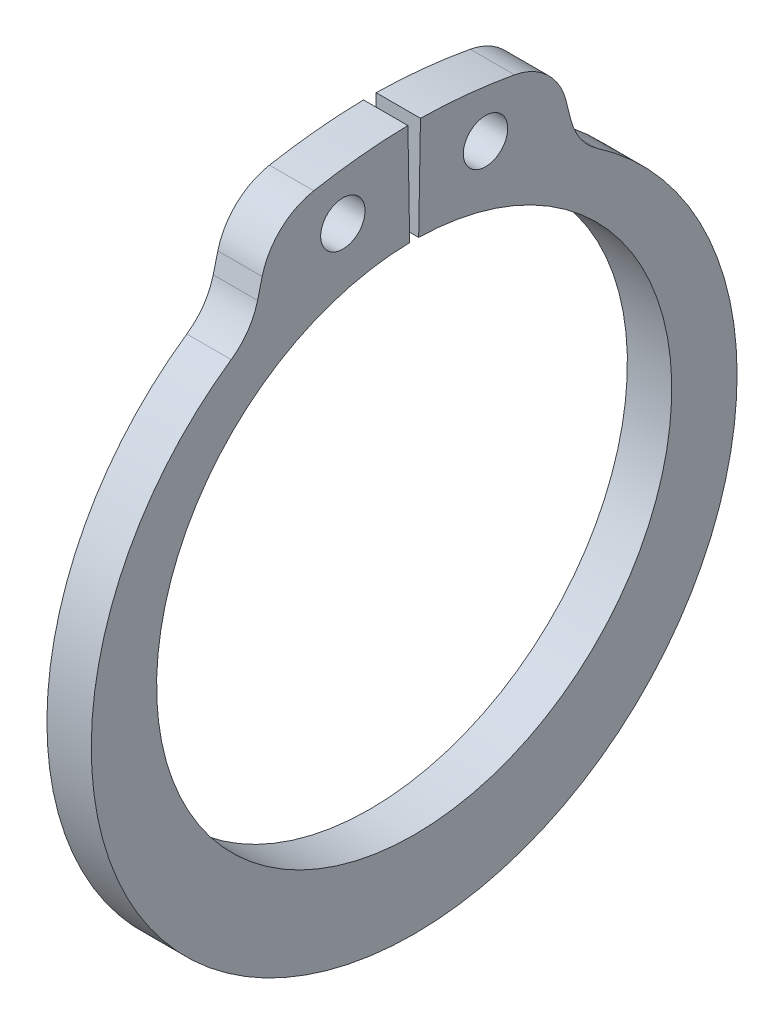
SolidWorks part; units mm, degrees
material "Cast Carbon Steel"
ref_plane "Front" through (0, 0, 0) normal (0, 0, 1) x (1, 0, 0)
ref_plane "Top" through (0, 0, 0) normal (0, 1, 0) x (1, 0, 0)
ref_plane "Right" through (0, 0, 0) normal (1, 0, 0) x (0, 0, -1)
sketch "Sketch1" plane through (0, 0, 0) normal (1, 0, 0) x (0, 0, -1)
  line L0 (0, 0) -> (0, 11.5062) construction
  line L1 (-0.2008, 11.5044) -> (-0.2806, 16.0758)
  line L2 (-0.2806, 16.0758) -> (-6.1704, 15.9729) construction
  line L3 (-6.1704, 15.9729) -> (-7.2765, 11.5368) construction
  line L4 (0.2806, 16.0758) -> (0.2008, 11.5044)
  line L5 (0.2806, 16.0758) -> (6.1704, 15.9729) construction
  line L6 (6.1704, 15.9729) -> (7.2765, 11.5368) construction
  line L7 (-7.2765, 11.5368) -> (-6.1383, 9.7321) construction
  line L8 (7.2765, 11.5368) -> (6.1383, 9.7321) construction
  line L9 (0, -11.5062) -> (0, -15.3416) construction
  line L10 (-6.1704, 15.9729) -> (-0.2008, 11.5044) construction
  line L11 (-11.5062, 0) -> (11.5062, 0) construction
  line L12 (0, 11.5062) -> (0, 16.0782) construction
  line L13 (6.3535, 15.2385) -> (7.2765, 11.5368)
  line L14 (-6.3535, 15.2385) -> (-7.2765, 11.5368)
  circle A0 centre (0, 0) radius 11.5062 construction
  arc A1 (-0.2008, 11.5044) -> (0.2008, 11.5044) centre (0, 0) ccw
  circle A2 centre (0, -0.9175) radius 14.4241 construction
  circle A3 centre (0, 0) radius 16.51 construction
  circle A4 centre (-3.1856, 13.7387) radius 0.9906
  circle A5 centre (3.1856, 13.7387) radius 0.9906
  arc A6 (-7.2765, 11.5368) -> (7.2765, 11.5368) centre (0, -0.9175) ccw
  arc A7 (0.2806, 16.0758) -> (6.3535, 15.2385) centre (-0.168, -9.6219) cw
  arc A8 (-0.2806, 16.0758) -> (-6.3535, 15.2385) centre (0.168, -9.6219) ccw
  dimension "D1" = 75
  dimension "A" = 23.0124
  dimension "L" = 33.02
  dimension "Hole" = 1.9812
  dimension "Smin" = 2.1336
  dimension "Smax" = 3.8354
  dimension "H" = 4.572
  dimension "Angle" = 1
extrude "Extrude1" add sketch "Sketch1" along normal mid plane 1.9812
fillet "Fillet1" radius 2.921 4 edges at (0, 11.5368, 7.2765) (0, 15.2385, 6.3535) (0, 15.2385, -6.3535) (0, 11.5368, -7.2765)
sketch "Sketch2" plane through (0, 0, 0) normal (0, 0, 1) x (1, 0, 0)
  line L0 (-5.461, 0) -> (16.383, 0)
  line L1 (16.383, 0) -> (16.383, -12.7)
  line L3 (16.383, -12.7) -> (1.0922, -12.7)
  line L4 (1.0922, -12.7) -> (1.0922, -11.9126)
  line L5 (1.0922, -11.9126) -> (-1.0922, -11.9126)
  line L6 (-1.0922, -11.9126) -> (-1.0922, -12.7)
  line L7 (-1.0922, -12.7) -> (-5.461, -12.7) construction
  line L8 (-5.461, -12.7) -> (-5.461, 0) construction
  line L9 (0, -11.9126) -> (0, 0) construction
  line L10 (16.383, 0) -> (14.0551, 0) construction
  line L11 (-1.0922, -12.7) -> (-5.0673, -12.7)
  line L12 (-5.0673, -12.7) -> (-5.461, -12.3063)
  line L13 (-5.461, -12.3063) -> (-5.461, 0)
  point P14 (-1.0922, -12.3063)
  dimension "Dg" = 23.8252
  dimension "Ds" = 25.4
  dimension "D2" = 21.844
  dimension "W" = 2.1844
  dimension "D3" = 5.461
  dimension "D4" = 45
revolve "Revolve1" [suppressed] add sketch "Sketch2" angle 360 about L10
equation "\"D2@Sketch2\" = \"W@Sketch2\"*10"
equation "\"D3@Sketch2\" = \"D2@Sketch2\"/4"
